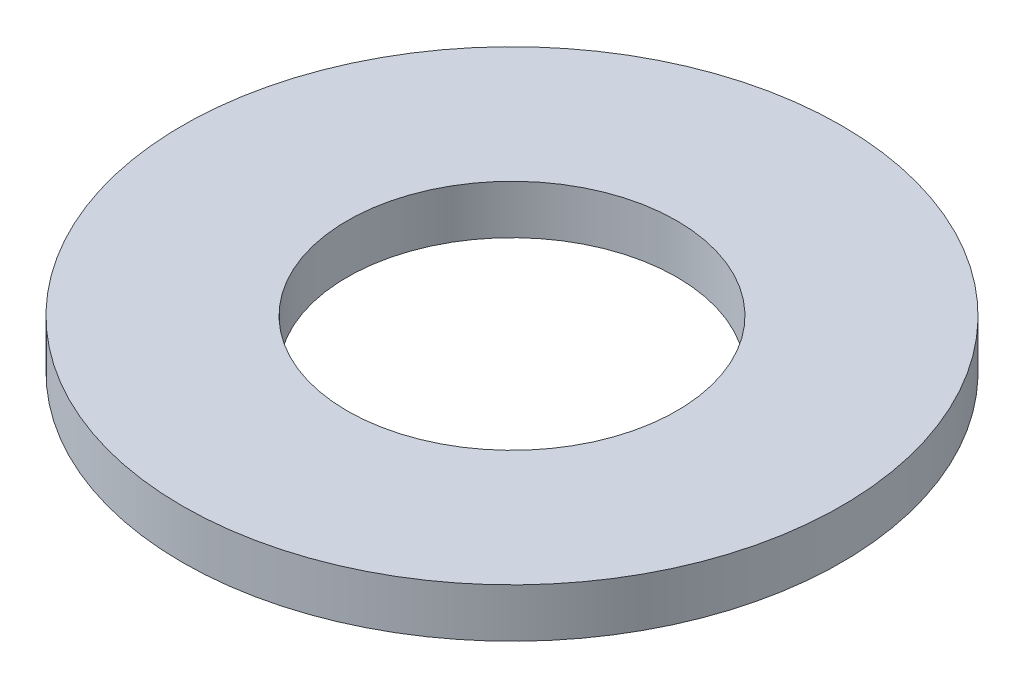
SolidWorks part; units mm, degrees
material "AISI 1020 Steel, Cold Rolled"
ref_plane "Front Plane" through (0, 0, 0) normal (0, 0, 1) x (1, 0, 0)
ref_plane "Top Plane" through (0, 0, 0) normal (0, 1, 0) x (1, 0, 0)
ref_plane "Right Plane" through (0, 0, 0) normal (1, 0, 0) x (0, 0, -1)
sketch "Sketch1" plane through (0, 0, 0) normal (0, 1, 0) x (1, 0, 0)
  circle A0 centre (0, 0) radius 4.3688
  circle A1 centre (0, 0) radius 8.7376
  dimension "ID" = 8.7376
  dimension "OD" = 17.4752
sketch "Sketch2" plane through (0, 0, 0) normal (1, 0, 0) x (0, 0, -1)
  line L1 (-8.7376, 0.6477) -> (8.7376, 0.6477)
  line L2 (-8.7376, 0.6477) -> (-8.7376, -0.6477)
  line L3 (-8.7376, -0.6477) -> (8.7376, -0.6477)
  line L4 (8.7376, 0.6477) -> (8.7376, -0.6477)
  line L5 (-8.7376, 0.6477) -> (8.7376, -0.6477) construction
  line L6 (-8.7376, -0.6477) -> (8.7376, 0.6477) construction
  point P0 (0, 0)
  point P6 (8.7376, 0)
  point P7 (-8.7376, 0)
  dimension "Thickness Range [Min]" = 1.2954
sketch "Sketch3" plane through (0, 0, 0) normal (0, 1, 0) x (1, 0, 0)
  circle A0 centre (0, 0) radius 8.7376
  circle A1 centre (0, 0) radius 4.3688
  circle A2 centre (0, 0) radius 8.7376 construction
  circle A3 centre (0, 0) radius 4.3688 construction
extrude "Boss-Extrude1" add sketch "Sketch3" along normal up to vertex (0.6477 mm away) and the other way up to vertex (0.6477 mm away) up to point (0, 0.6477, -8.7376) other way up to point (0, -0.6477, -8.7376)
